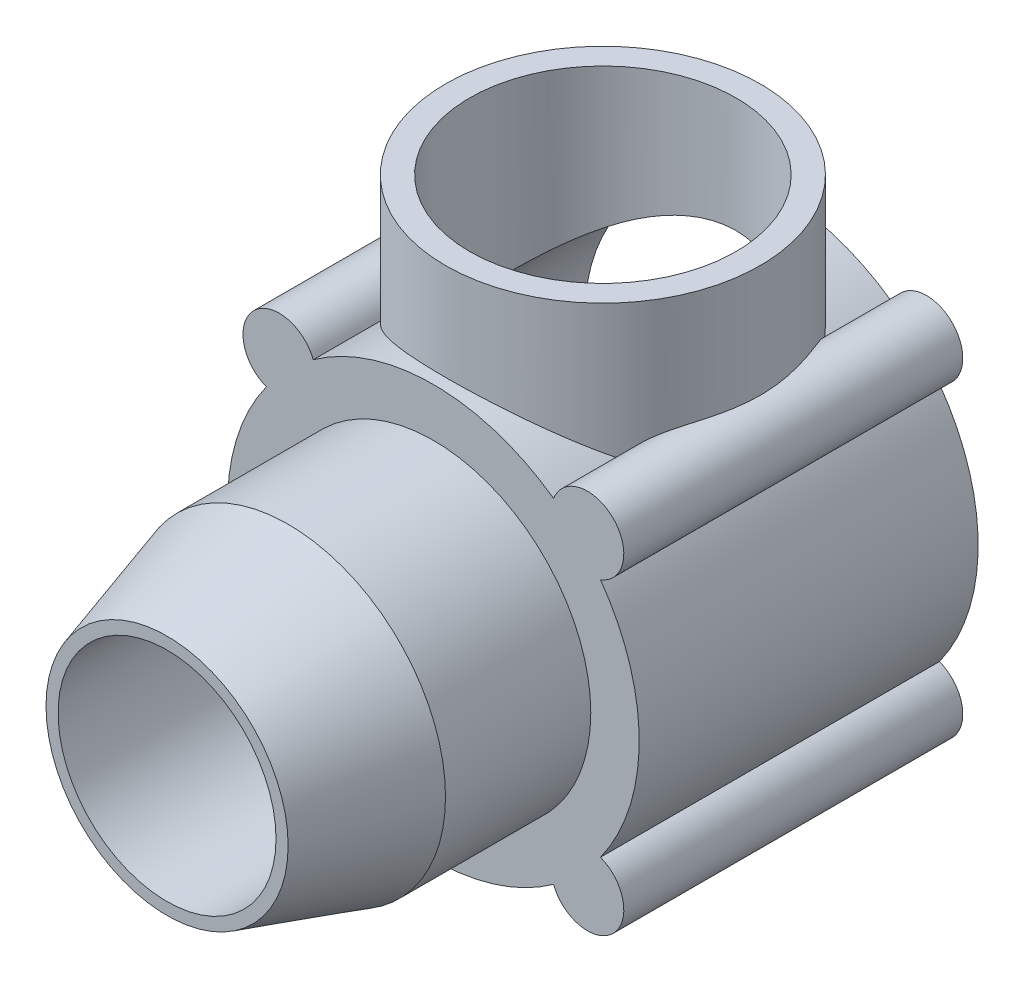
SolidWorks part; units mm, degrees
ref_plane "Front Plane" through (0, 0, 0) normal (0, 0, 1) x (1, 0, 0)
ref_plane "Top Plane" through (0, 0, 0) normal (0, 1, 0) x (1, 0, 0)
ref_plane "Right Plane" through (0, 0, 0) normal (1, 0, 0) x (0, 0, -1)
sketch "Sketch1" plane through (0, 0, 0) normal (0, 0, 1) x (1, 0, 0)
  circle A0 centre (0, 0) radius 17
  dimension "D1" = 34
extrude "Boss-Extrude1" add sketch "Sketch1" along normal mid plane 28
sketch "Sketch2" plane through (0, 0, 14) normal (0, 0, 1) x (1, 0, 0)
  circle A0 centre (0, 0) radius 13
  dimension "D1" = 26
extrude "Boss-Extrude2" add sketch "Sketch2" along normal blind 22
sketch "Sketch3" plane through (0, 0, 0) normal (0, 1, 0) x (1, 0, 0)
  line L0 (17, 14) -> (-17, 14) construction
  circle A0 centre (0, 0) radius 13
  dimension "D1" = 26
  dimension "D2" = 14
extrude "Boss-Extrude3" add sketch "Sketch3" along normal blind 25
sketch "Sketch4" plane through (0, 0, -14) normal (0, 0, -1) x (-1, 0, 0)
  circle A0 centre (0, 0) radius 15.5
  dimension "D1" = 31
extrude "Cut-Extrude1" cut sketch "Sketch4" against normal blind 25
sketch "Sketch5" plane through (0, 0, 36) normal (0, 0, 1) x (1, 0, 0)
  circle A0 centre (0, 0) radius 9
  dimension "D1" = 18
extrude "Cut-Extrude2" cut sketch "Sketch5" against normal blind 25
chamfer "Chamfer2" distance 10 distance2 3 1 edges at (13, 0, 36)
sketch "Sketch7" plane through (0, 0, -14) normal (0, 0, -1) x (-1, 0, 0)
  line L0 (0, 0) -> (-20.8486, 20.8486) construction
  line L1 (0, 0) -> (0, 29.5733) construction
  arc A0 (-9.8194, 11.9929) -> (-11.9929, 9.8194) centre (-12.7279, 12.7279) ccw
  circle A1 centre (0, 0) radius 15.5 construction
  arc A2 (-9.8194, 11.9929) -> (-11.9929, 9.8194) centre (0, 0) ccw
  dimension "D1" = 6
  dimension "D2" = 45
  dimension "D3" = 18
extrude "Boss-Extrude4" add sketch "Sketch7" against normal up to surface (28 mm away) up to face at (17, 0, 14)
pattern_circular "CirPattern1" count 4 over 360 about axis through (0, 0, 0) along (0, 0, 1) of "Boss-Extrude4"
sketch "Sketch6" plane through (0, 25, 0) normal (0, 1, 0) x (1, 0, 0)
  circle A0 centre (0, 0) radius 11
  dimension "D1" = 22
extrude "Cut-Extrude3" cut sketch "Sketch6" against normal blind 25
hole_wizard "Tap Drill for M3x0.5 Tap1" positions "Sketch10" profile "Sketch9" hole size "M3x0.5" standard "ANSI Metric"
sketch "Sketch10" plane through (0, 0, -14) normal (0, 0, -1) x (-1, 0, 0)
  point P0 (-12.7279, 12.7279)
sketch "Sketch9" plane through (12.7279, 12.7279, -14) normal (1, 0, 0) x (0, 1, 0)
  line L0 (0, 0) -> (0, 9.7511)
  line L1 (0, 9.7511) -> (1.25, 9)
  line L2 (1.25, 9) -> (1.25, 0.25)
  line L3 (1.25, 0.25) -> (1.5, 0)
  line L5 (1.5, 0) -> (0, 0)
  line L6 (-1.25, 0.25) -> (-1.5, 0) construction
  line L10 (0, 9.7511) -> (-1.25, 9) construction
  line L11 (0, -6.35) -> (0, 107.95) construction
  dimension "Hole Dia." = 2.5
  dimension "Hole Depth" = 9
  dimension "Near C'Sink Dia." = 3
  dimension "Near C'Sink Angle" = 90
  dimension "Drill Angle" = 118
pattern_circular "CirPattern2" count 4 over 360 about axis through (0, 0, 0) along (0, 0, 1) of "Tap Drill for M3x0.5 Tap1"
